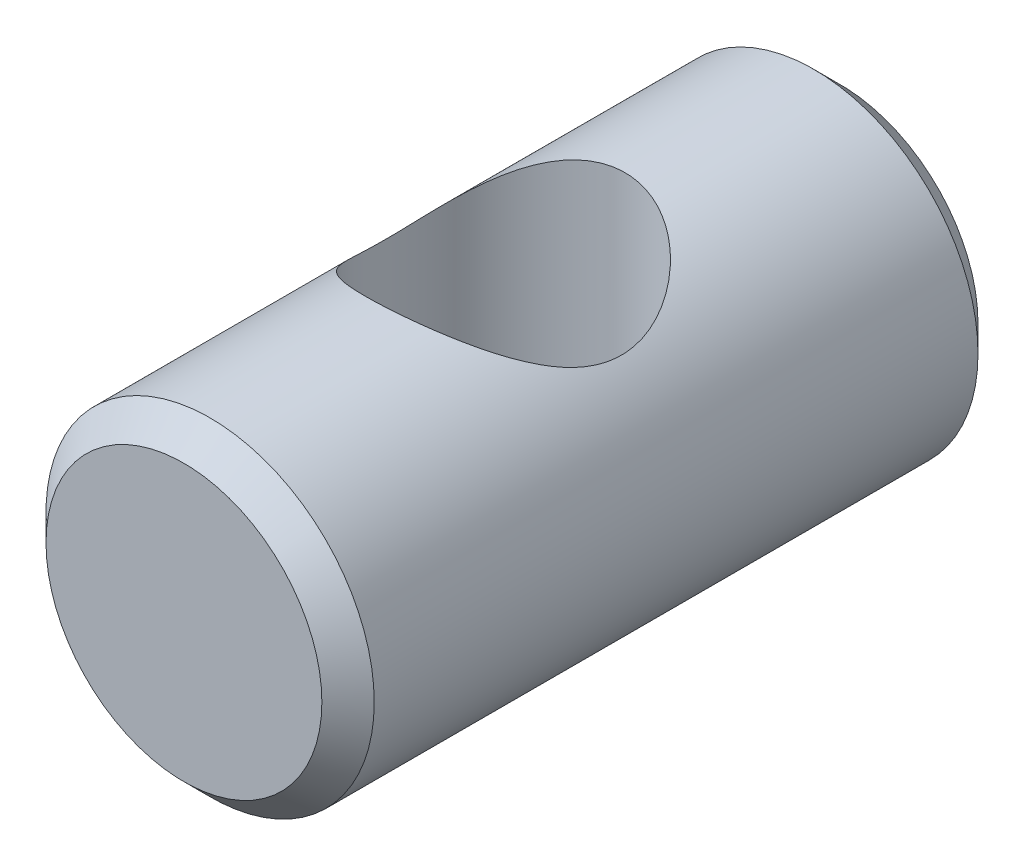
SolidWorks part; units mm, degrees
ref_plane "Front Plane" through (0, 0, 0) normal (0, 0, 1) x (1, 0, 0)
ref_plane "Top Plane" through (0, 0, 0) normal (0, 1, 0) x (1, 0, 0)
ref_plane "Right Plane" through (0, 0, 0) normal (1, 0, 0) x (0, 0, -1)
sketch "Sketch1" plane through (0, 0, 0) normal (0, 0, 1) x (1, 0, 0)
  circle A0 centre (0, 0) radius 4.765
  dimension "D1" = 9.53
extrude "Boss-Extrude1" add sketch "Sketch1" along normal mid plane 19.05
chamfer "Chamfer1" distance 0.76 angle 45 2 edges at (4.765, 0, -9.525) (4.765, 0, 9.525)
sketch "Sketch2" plane through (0, 0, 0) normal (0, 1, 0) x (1, 0, 0)
  circle A0 centre (-0.25, 0) radius 3.43
  point P2 (0, 0)
  dimension "D1" = 6.86
  dimension "D2" = 0.25
extrude "Cut-Extrude1" cut sketch "Sketch2" against normal through all both and the other way through all
